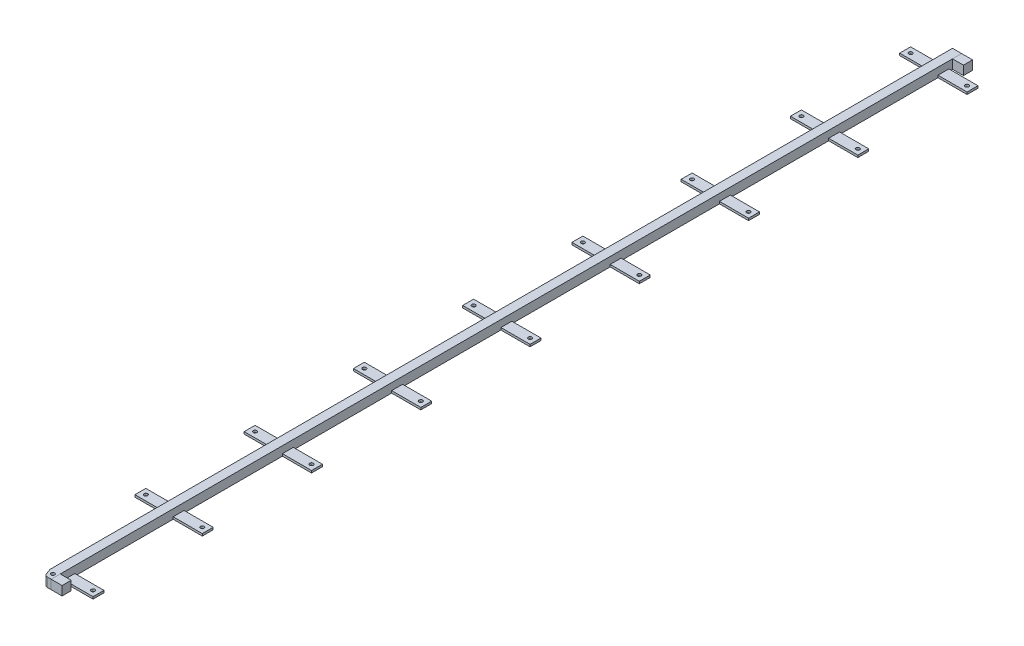
SolidWorks part; units mm, degrees
material "普通碳钢"
ref_plane "前视基准面" through (0, 0, 0) normal (0, 0, 1) x (1, 0, 0)
ref_plane "上视基准面" through (0, 0, 0) normal (0, 1, 0) x (1, 0, 0)
ref_plane "右视基准面" through (0, 0, 0) normal (1, 0, 0) x (0, 0, -1)
sketch "草图1" plane through (0, 0, 0) normal (0, 1, 0) x (1, 0, 0)
  line L0 (0, 0) -> (0, 2500)
  line L1 (0, 2500) -> (25, 2500)
  line L2 (25, 2500) -> (25, 0)
  line L3 (25, 0) -> (0, 0)
  dimension "D1" = 2500
  dimension "D2" = 25
extrude "凸台-拉伸1" add sketch "草图1" along normal blind 25
sketch "草图2" plane through (0, 0, 0) normal (0, 1, 0) x (1, 0, 0)
  line L1 (25, 0) -> (55, 0)
  line L2 (25, 0) -> (25, 25)
  line L3 (25, 25) -> (55, 25)
  line L4 (55, 0) -> (55, 25)
  dimension "D1" = 30
  dimension "D2" = 25
extrude "凸台-拉伸2" add sketch "草图2" along normal blind 25 separate body
chamfer "倒角1" distance 22 distance2 8 1 edges at (0, 12.5, 0)
fillet "圆角2" radius 10 2 edges at (0, 12.5, -22) (8, 12.5, 0)
sketch "草图3" plane through (0, 0, -2500) normal (0, 0, -1) x (-1, 0, 0)
  line L1 (-25, 25) -> (-55, 25)
  line L2 (-25, 25) -> (-25, 0)
  line L3 (-25, 0) -> (-55, 0)
  line L4 (-55, 25) -> (-55, 0)
  dimension "D1" = 30
  dimension "D2" = 25
extrude "凸台-拉伸3" add sketch "草图3" against normal blind 25 separate body
sketch "草图4" plane through (0, 0, 0) normal (0, 1, 0) x (1, 0, 0)
  line L0 (0, 2500) -> (0, 23.7617) construction
  line L5 (0, 2465) -> (-80, 2465)
  line L6 (0, 2465) -> (0, 2435)
  line L7 (0, 2435) -> (-80, 2435)
  line L8 (-80, 2465) -> (-80, 2435)
  line L9 (25, 0) -> (25, 2500) construction
  line L10 (25, 2465) -> (105, 2465)
  line L11 (25, 2465) -> (25, 2435)
  line L12 (25, 2435) -> (105, 2435)
  line L13 (105, 2465) -> (105, 2435)
  line L14 (25, 2500) -> (55, 2500) construction
  line L19 (25, 2500) -> (0, 2500) construction
  line L20 (105, 2450) -> (-20, 2450) construction
  circle A0 centre (90, 2450) radius 5
  circle A1 centre (-65, 2450) radius 5
  point P22 (25, 2450)
  dimension "D7" = 65
  dimension "D9" = 10
  dimension "D1" = 30
  dimension "D2" = 30
  dimension "D3" = 80
  dimension "D4" = 80
  dimension "D5" = 35
  dimension "D6" = 35
  dimension "D8" = 65
extrude "凸台-拉伸4" add sketch "草图4" along normal blind 6 separate body
pattern_linear "阵列(线性)1" count 9 spacing 300 along (0, 0, 1) of "凸台-拉伸4"
sketch "草图5" plane through (0, 25, 0) normal (0, 1, 0) x (1, 0, 0)
  line L0 (25, 0) -> (25, 2500) construction
  line L1 (15.0043, 0) -> (25, 0) construction
  circle A0 centre (15, 15) radius 5
  dimension "D1" = 10
  dimension "D2" = 10
  dimension "D3" = 15
extrude "切除-拉伸1" cut sketch "草图5" against normal up to next (25 mm away)
sketch "草图6" plane through (0, 6, 0) normal (0, 1, 0) x (1, 0, 0)
  line L0 (-80, 35) -> (0, 35) construction
  line L1 (-80, 65) -> (0, 65)
  line L2 (-80, 65) -> (-80, 35)
  line L3 (-80, 35) -> (0, 35)
  line L4 (0, 65) -> (0, 35)
  line L5 (0, 65) -> (-80, 65) construction
  line L6 (-80, 65) -> (-80, 35) construction
  line L7 (0, 35) -> (0, 65) construction
extrude "切除-拉伸2" cut sketch "草图6" against normal blind 10
